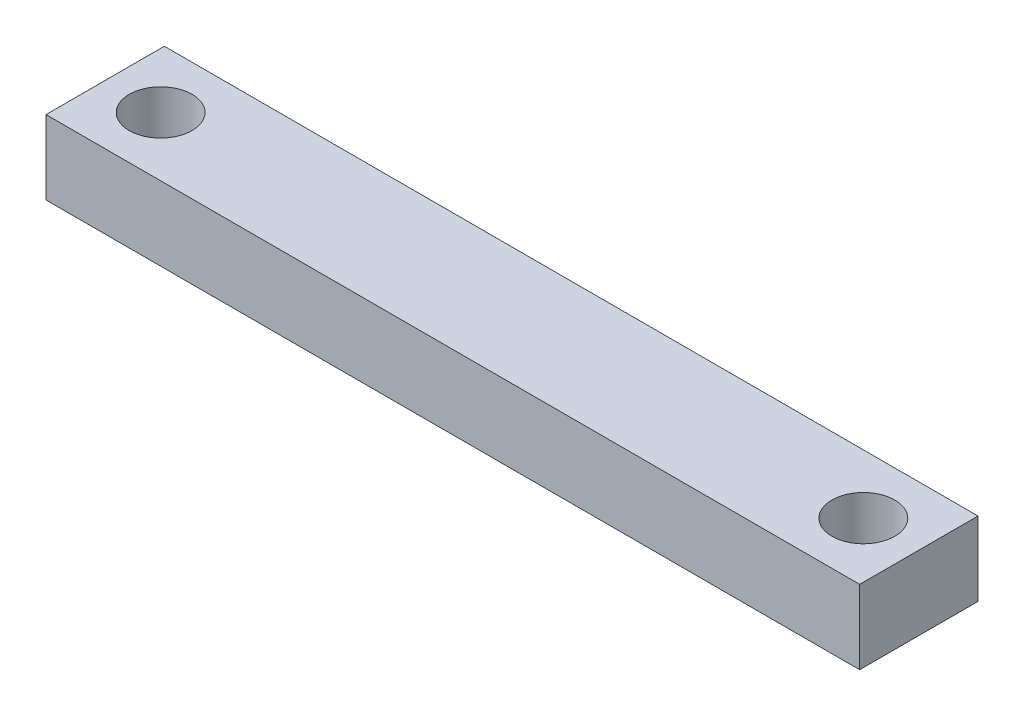
SolidWorks part; units mm, degrees
ref_plane "前视基准面" through (0, 0, 0) normal (0, 0, 1) x (1, 0, 0)
ref_plane "上视基准面" through (0, 0, 0) normal (0, 1, 0) x (1, 0, 0)
ref_plane "右视基准面" through (0, 0, 0) normal (1, 0, 0) x (0, 0, -1)
sketch "草图1" plane through (0, 0, 0) normal (0, 1, 0) x (1, 0, 0)
  line L0 (-47.5, 0) -> (47.5, 0) construction
  line L1 (-55, 8) -> (55, 8)
  line L2 (-55, 8) -> (-55, -8)
  line L3 (-55, -8) -> (55, -8)
  line L4 (55, 8) -> (55, -8)
  line L5 (-55, 8) -> (55, -8) construction
  line L6 (-55, -8) -> (55, 8) construction
  line L7 (0, 28.872) -> (0, -21.3132) construction
  point P0 (0, 0)
  point P10 (0, 0)
  dimension "D1" = 110
  dimension "D2" = 16
  dimension "D3" = 95
extrude "凸台-拉伸1" add sketch "草图1" along normal blind 10
sketch "草图3" plane through (0, 10, 0) normal (0, 1, 0) x (1, 0, 0)
  line L0 (-47.5, 0) -> (47.5, 0) construction
  dimension "D1" = 95
hole_wizard "M10 螺纹孔1" positions "3D草图2" profile "草图4" tap size "M10" standard "GB"
sketch3d "3D草图2"
  point P0 (-47.5, 10, 0)
  point P3 (47.5, 10, 0)
sketch "草图4" plane through (-47.5, 10, 0) normal (1, 0, 0) x (0, 0, 1)
  line L0 (0, 0) -> (0, 27.0537)
  line L1 (0, 27.0537) -> (4.25, 24.5)
  line L2 (4.25, 24.5) -> (4.25, 0)
  line L5 (4.25, 0) -> (0, 0)
  line L10 (0, 27.0537) -> (-4.25, 24.5) construction
  line L11 (0, -6.35) -> (0, 107.95) construction
  dimension "螺纹孔钻头直径" = 8.5
  dimension "螺纹孔钻头深度" = 24.5
  dimension "导头角度" = 118
cosmetic thread "孔螺蚊线1" parameters "D1"=10, "D2"=10
cosmetic thread "孔螺蚊线2" parameters "D1"=10, "D2"=10
